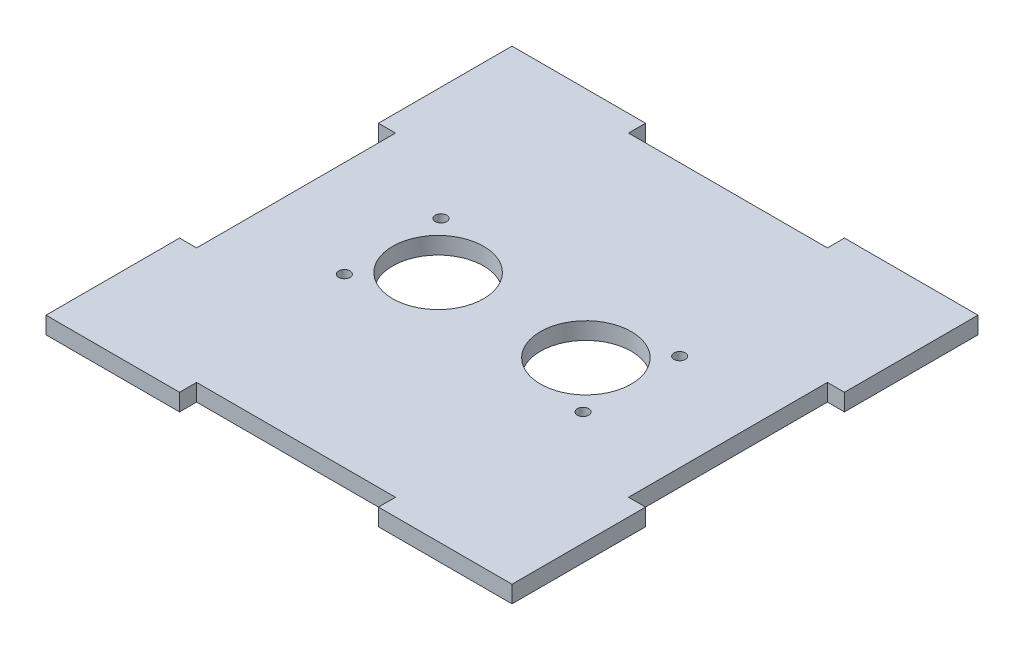
SolidWorks part; units mm, degrees
ref_plane "Front Plane" through (0, 0, 0) normal (0, 0, 1) x (1, 0, 0)
ref_plane "Top Plane" through (0, 0, 0) normal (0, 1, 0) x (1, 0, 0)
ref_plane "Right Plane" through (0, 0, 0) normal (1, 0, 0) x (0, 0, -1)
sketch "Sketch1" plane through (0, 0, 0) normal (0, 1, 0) x (1, 0, 0)
  line L0 (0, 38) -> (0, -38) construction
  line L1 (-41, -41) -> (-17.5, -41)
  line L2 (-41, -41) -> (-41, -17.5)
  line L3 (-41, 41) -> (-17.5, 41)
  line L4 (41, -41) -> (41, -17.5)
  line L5 (-41, -41) -> (41, 41) construction
  line L6 (-41, 41) -> (41, -41) construction
  line L11 (-41, 17.5) -> (-38, 17.5)
  line L12 (-38, 17.5) -> (-38, -17.5)
  line L13 (-35, 0) -> (38, 0) construction
  line L26 (17.5, 41) -> (41, 41)
  line L27 (41, 17.5) -> (41, 41)
  line L28 (17.5, -41) -> (41, -41)
  line L29 (-41, 17.5) -> (-41, 41)
  line L30 (-38, -17.5) -> (-41, -17.5)
  line L31 (-17.5, 41) -> (-17.5, 38)
  line L32 (-17.5, 38) -> (17.5, 38)
  line L33 (17.5, 38) -> (17.5, 41)
  line L34 (41, 17.5) -> (38, 17.5)
  line L35 (38, 17.5) -> (38, -17.5)
  line L36 (38, -17.5) -> (41, -17.5)
  line L37 (17.5, -41) -> (17.5, -38)
  line L38 (17.5, -38) -> (-17.5, -38)
  line L39 (-17.5, -38) -> (-17.5, -41)
  point P0 (0, 0)
  point P6 (0, 0)
  dimension "D1" = 3
  dimension "D2" = 82
  dimension "D3" = 3
  dimension "D4" = 82
  dimension "D5" = 3
  dimension "D6" = 3
extrude "Boss-Extrude1" add sketch "Sketch1" along normal blind 3
sketch "Sketch2" plane through (0, 3, 0) normal (0, 1, 0) x (1, 0, 0)
  line L0 (0, 10) -> (0, -10) construction
  line L5 (-22.5, 10) -> (22.5, 10) construction
  line L6 (-22.5, 10) -> (-22.5, -10) construction
  line L7 (-22.5, -10) -> (22.5, -10) construction
  line L8 (22.5, 10) -> (22.5, -10) construction
  line L9 (-22.5, 10) -> (22.5, -10) construction
  line L10 (-22.5, -10) -> (22.5, 10) construction
  line L11 (-22.5, 0) -> (22.5, 0) construction
  circle A1 centre (-13, 0) radius 8
  circle A3 centre (-21, 8.5) radius 1
  circle A4 centre (-21, -8.5) radius 1
  circle A5 centre (21, -8.5) radius 1
  circle A6 centre (21, 8.5) radius 1
  circle A7 centre (13, 0) radius 8
  point P0 (0, 0)
  dimension "D3" = 2
  dimension "D7" = 16
  dimension "D1" = 45
  dimension "D2" = 20
  dimension "D4" = 1.5
  dimension "D5" = 1.5
  dimension "D6" = 13
extrude "Cut-Extrude1" cut sketch "Sketch2" against normal blind 3
